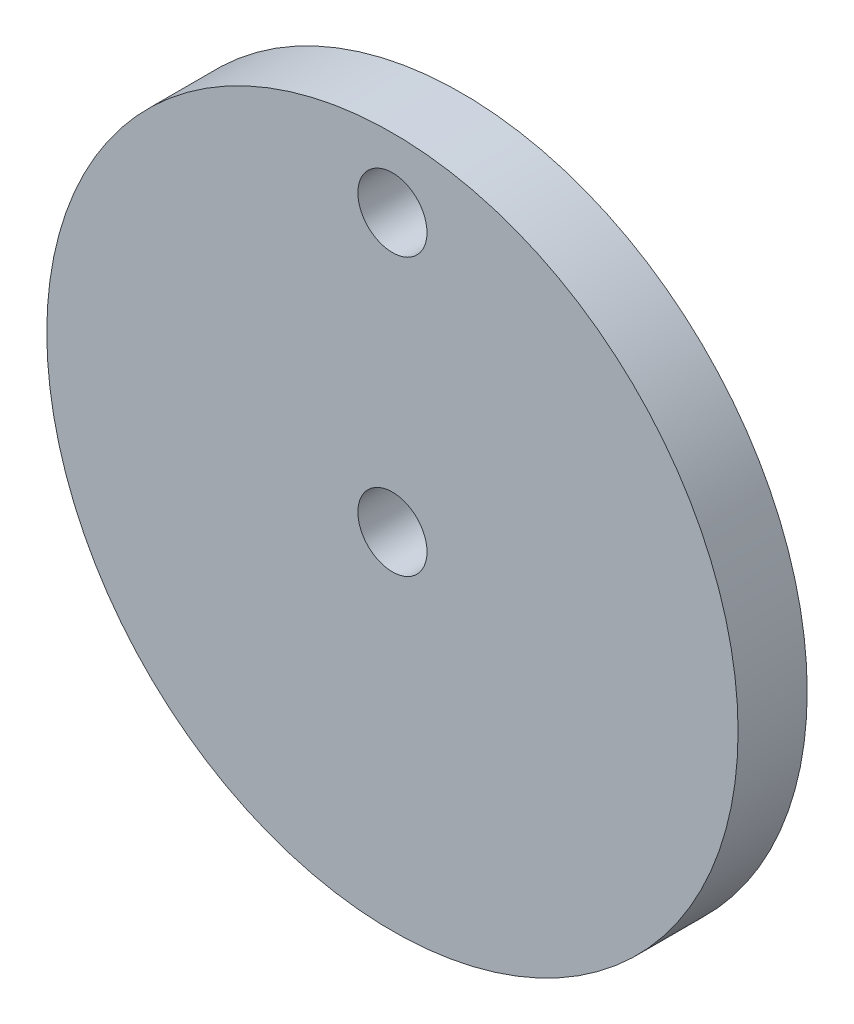
SolidWorks part; units mm, degrees
ref_plane "Front Plane" through (0, 0, 0) normal (0, 0, 1) x (1, 0, 0)
ref_plane "Top Plane" through (0, 0, 0) normal (0, 1, 0) x (1, 0, 0)
ref_plane "Right Plane" through (0, 0, 0) normal (1, 0, 0) x (0, 0, -1)
sketch "Sketch1" plane through (0, 0, 0) normal (0, 0, 1) x (1, 0, 0)
  circle A0 centre (0, 0) radius 5
  circle A1 centre (0, 0) radius 50
  circle A2 centre (0, 40) radius 5
  dimension "D1" = 10
  dimension "D2" = 100
  dimension "D3" = 10
  dimension "D4" = 40
extrude "Boss-Extrude1" add sketch "Sketch1" along normal blind 10
